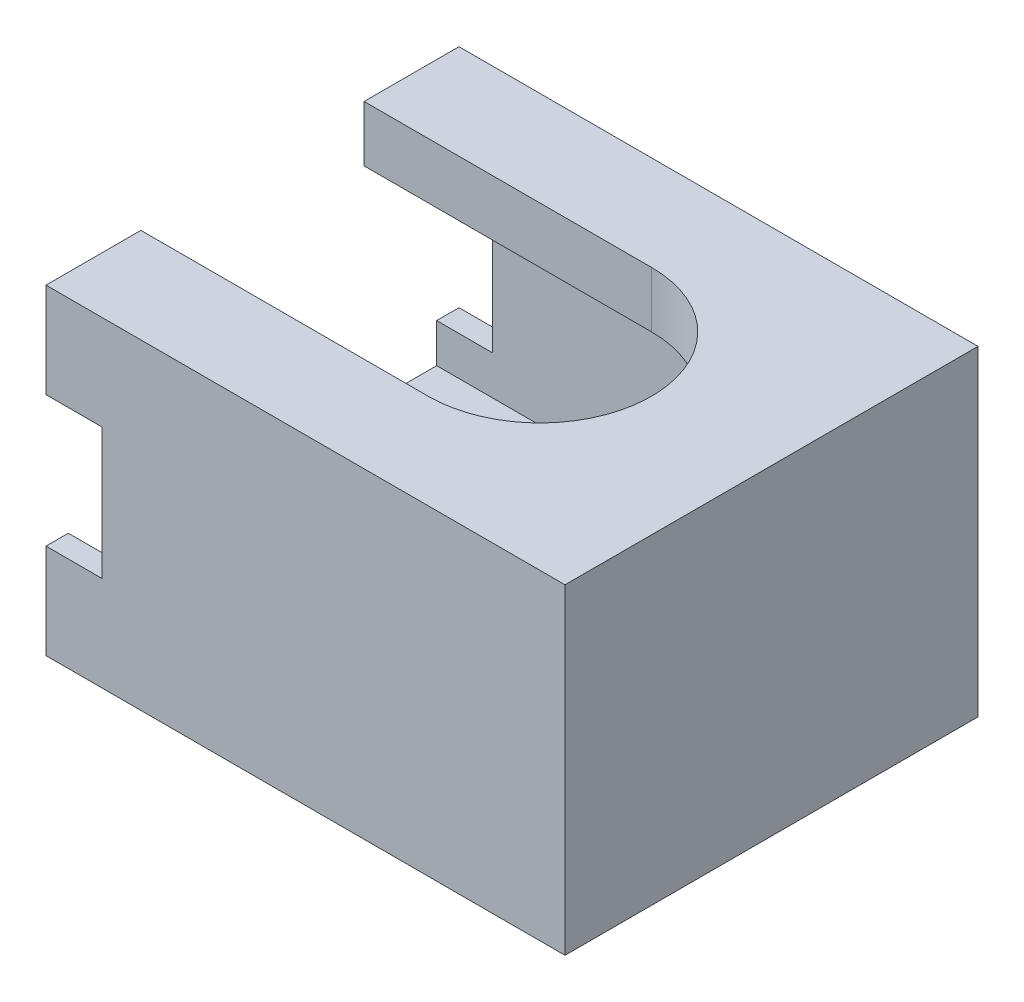
SolidWorks part; units mm, degrees
ref_plane "Front Plane" through (0, 0, 0) normal (0, 0, 1) x (1, 0, 0)
ref_plane "Top Plane" through (0, 0, 0) normal (0, 1, 0) x (1, 0, 0)
ref_plane "Right Plane" through (0, 0, 0) normal (1, 0, 0) x (0, 0, -1)
sketch "Sketch3" plane through (0, 0, 0) normal (0, 1, 0) x (1, 0, 0)
  line L11 (8.3, -7.4) -> (8.3, 7.4)
  line L12 (7.5, -6.6) -> (-7.5, -6.6)
  line L13 (7.5, -6.6) -> (7.5, 6.6)
  line L14 (7.5, 6.6) -> (-7.5, 6.6)
  line L15 (-7.5, -6.6) -> (-7.5, 6.6) construction
  line L16 (7.5, -6.6) -> (-7.5, 6.6) construction
  line L17 (7.5, 6.6) -> (-7.5, -6.6) construction
  line L18 (8.3, 7.4) -> (-8.3, 7.4)
  line L19 (-8.3, -7.4) -> (-8.3, 7.4) construction
  line L20 (8.3, -7.4) -> (-8.3, -7.4)
  line L21 (-8.3, 7.4) -> (-8.3, 6.6)
  line L22 (-8.3, 6.6) -> (-7.5, 6.6)
  line L23 (-7.5, -6.6) -> (-8.3, -6.6)
  line L24 (-8.3, -6.6) -> (-8.3, -7.4)
  point P0 (0, 0)
  point P10 (0, 0)
  dimension "D1" = 13.2
  dimension "D2" = 0.8
  dimension "D3" = 15
extrude "Boss-Extrude1" add sketch "Sketch3" along normal blind 7.5
sketch "Sketch4" plane through (0, 0, 0) normal (0, -1, 0) x (1, 0, 0)
  line L2 (-8.3, -7.4) -> (8.3, -7.4)
  line L3 (-8.3, -7.4) -> (-8.3, 7.4)
  line L4 (-8.3, 7.4) -> (8.3, 7.4)
  line L5 (8.3, -7.4) -> (8.3, 7.4)
  line L6 (-8.3, -7.4) -> (8.3, 7.4) construction
  line L7 (-8.3, 7.4) -> (8.3, -7.4) construction
  point P2 (0, 0)
extrude "Boss-Extrude2" add sketch "Sketch4" along normal blind 2
sketch "Sketch5" plane through (0, 7.5, 0) normal (0, 1, 0) x (1, 0, 0)
  line L0 (-8.3, 4) -> (0, 4)
  line L1 (8.3, -7.4) -> (-8.3, -7.4)
  line L2 (8.3, -7.4) -> (8.3, 7.4)
  line L3 (8.3, 7.4) -> (-8.3, 7.4)
  line L4 (-8.3, -7.4) -> (-8.3, 7.4) construction
  line L5 (8.3, -7.4) -> (-8.3, 7.4) construction
  line L6 (8.3, 7.4) -> (-8.3, -7.4) construction
  line L7 (-8.3, -4) -> (0, -4)
  line L8 (-8.3, 7.4) -> (-8.3, 4)
  line L9 (-8.3, -4) -> (-8.3, -7.4)
  arc A0 (0, 4) -> (0, -4) centre (0, 0) cw
  point P0 (0, 0)
  dimension "D1" = 4
extrude "Boss-Extrude3" add sketch "Sketch5" along normal blind 2
sketch "Sketch8" plane through (-8.3, 0, 0) normal (-1, 0, 0) x (0, 0, 1)
  line L0 (-4, 9.5) -> (-7.4, 9.5)
  line L1 (-7.4, 9.5) -> (-4, 9.5) construction
  line L2 (-7.4, 9.5) -> (-7.4, 6.1)
  line L3 (-7.4, 9.5) -> (-7.4, -2) construction
  line L4 (-7.4, 6.1) -> (-6.6, 6.1)
  line L5 (-6.6, 7.5) -> (-6.6, 0) construction
  line L6 (-6.6, 6.1) -> (-6.6, 7.5)
  line L7 (-6.6, 7.5) -> (-4, 7.5)
  line L8 (-6.6, 7.5) -> (-4, 7.5) construction
  line L9 (-4, 7.5) -> (-4, 9.5)
  line L10 (4, 9.5) -> (4, 7.5)
  line L11 (4, 9.5) -> (7.4, 9.5) construction
  line L12 (-6.6, 7.5) -> (6.6, 7.5) construction
  line L13 (4, 7.5) -> (6.6, 7.5)
  line L14 (6.6, 7.5) -> (6.6, 6.1)
  line L15 (6.6, 6.1) -> (7.4, 6.1)
  line L16 (7.4, 9.5) -> (7.4, -2) construction
  line L17 (7.4, 6.1) -> (7.4, 9.5)
  line L18 (7.4, 9.5) -> (4, 9.5)
  line L19 (6.6, 1.4) -> (7.4, 1.4)
  line L20 (6.6, 7.5) -> (6.6, 0) construction
  line L21 (7.4, 1.4) -> (7.4, -2)
  line L22 (7.4, -2) -> (4, -2)
  line L23 (7.4, -2) -> (-7.4, -2) construction
  line L24 (4, -2) -> (4, 0)
  line L25 (-6.6, 0) -> (6.6, 0) construction
  line L26 (4, 0) -> (6.6, 0)
  line L27 (6.6, 0) -> (6.6, 1.4)
  line L28 (-7.4, 1.4) -> (-6.6, 1.4)
  line L29 (-6.6, 7.5) -> (-6.6, 0) construction
  line L30 (-6.6, 1.4) -> (-6.6, 0)
  line L31 (-6.6, 0) -> (-4, 0)
  line L32 (-4, 0) -> (-4, -2)
  line L33 (-4, -2) -> (-7.4, -2)
  line L34 (-7.4, -2) -> (-7.4, 1.4)
  dimension "D1" = 3.4
extrude "Boss-Extrude6" add sketch "Sketch8" along normal blind 2
